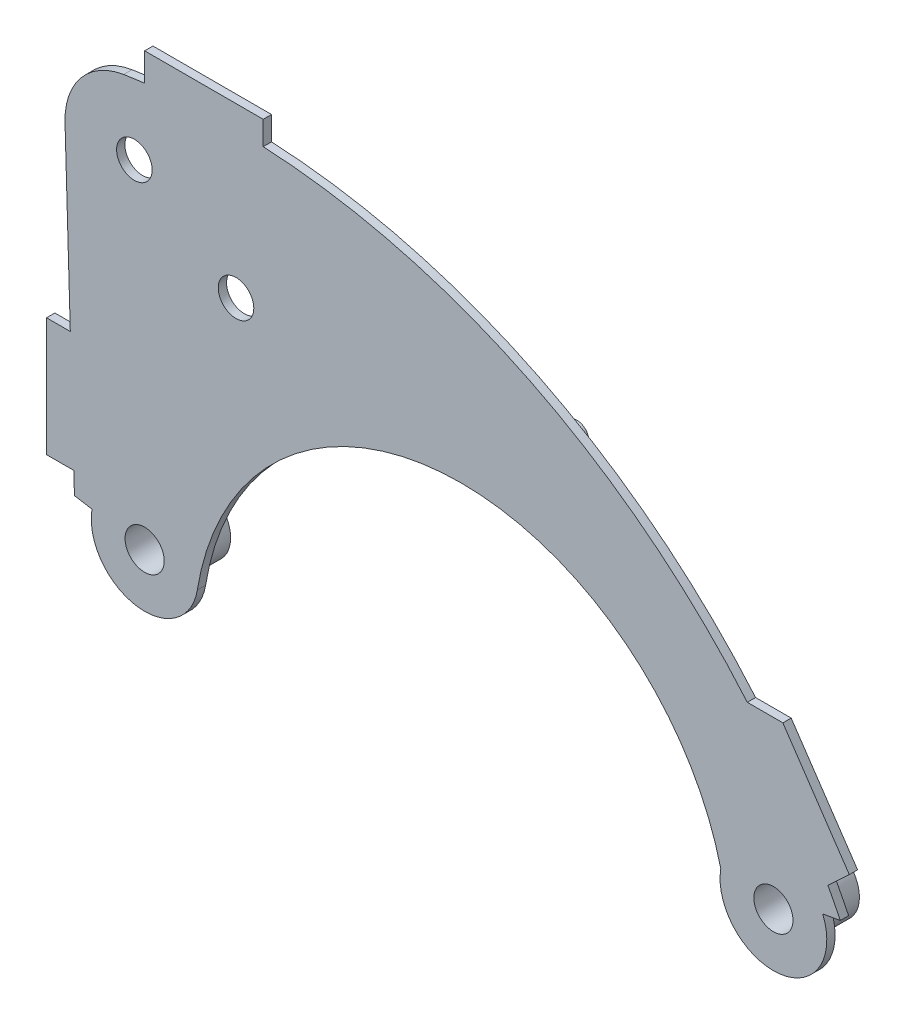
SolidWorks part; units mm, degrees
ref_plane "Front Plane" through (0, 0, 0) normal (0, 0, 1) x (1, 0, 0)
ref_plane "Top Plane" through (0, 0, 0) normal (0, 1, 0) x (1, 0, 0)
ref_plane "Right Plane" through (0, 0, 0) normal (1, 0, 0) x (0, 0, -1)
sketch "Sketch1" plane through (0, 0, 0) normal (0, 0, 1) x (1, 0, 0)
  line L0 (3.5714, 20.1522) -> (3.5714, -246.7943) construction
  line L1 (-308.017, 51.5444) -> (-322.8113, 54.0201)
  line L2 (3.2114, 1.0414) -> (684.3791, 1.0414) construction
  line L3 (3.2114, 1.0414) -> (-642.1053, 1.0414) construction
  line L4 (3.2114, 1.0414) -> (3.2114, 295.5408) construction
  line L5 (266.5683, 46.7848) -> (266.5683, 1.7848) construction
  line L6 (3.2114, 1.0414) -> (3.5714, 1.1081) construction
  line L7 (-263.6341, 44.1172) -> (-263.6341, -0.8828) construction
  line L8 (308.1159, 64.0706) -> (322.9429, 66.6583)
  line L9 (-263.6341, -0.8828) -> (3.2114, 1.0414)
  line L10 (-322.8113, 54.0201) -> (-330.7613, 322.7691)
  line L11 (3.2114, 1.0414) -> (3.5714, 1.1081)
  arc A0 (222.17, 54.1191) -> (-219.2092, 36.9459) centre (3.2114, 1.0414) ccw
  arc A1 (-308.017, 51.5444) -> (-219.2092, 36.9459) centre (-263.6341, 44.1172) ccw
  arc A4 (222.17, 54.1191) -> (308.1159, 64.0706) centre (266.5683, 46.7848) ccw
  circle A5 centre (-263.6341, 44.1172) radius 16.5
  circle A6 centre (266.5683, 46.7848) radius 16.5
  circle A9 centre (3.2114, 1.0414) radius 217.3
  arc A11 (-281.3271, 382.2962) -> (-330.7613, 322.7691) centre (-272.2869, 324.4989) ccw
  circle A12 centre (-272.2869, 324.4989) radius 15
  arc A14 (322.9429, 66.6583) -> (-281.3271, 382.2962) centre (-192.7071, -184.2846) ccw
  circle A15 centre (-186.5844, 266.4702) radius 15
  dimension "D1" = 90
  dimension "D2" = 0.413
  dimension "D5" = 10.5
  dimension "D6" = 267.3
extrude "Boss-Extrude3" add sketch "Sketch1" along normal blind 7 contours L8 A14 A11 A15 L10 L1 A1 A0 A4 A5 A6 | A11 A12
sketch "Sketch2" plane through (0, 0, 7) normal (0, 0, 1) x (1, 0, 0)
  circle A0 centre (-263.6341, 44.1172) radius 27.5
  circle A2 centre (-263.6341, 44.1172) radius 16.5
  circle A3 centre (266.5683, 46.7848) radius 16.5
  circle A4 centre (266.5683, 46.7848) radius 27.5
extrude "Boss-Extrude4" add sketch "Sketch2" against normal blind 45
sketch "Sketch3" plane through (0, 0, 0) normal (0, 0, -1) x (-1, 0, 0)
  line L0 (-198.3557, 159.2041) -> (-104.6899, 234.2155)
  arc A0 (-198.3557, 159.2041) -> (-104.6899, 234.2155) centre (-151.5228, 196.7098) cw
  arc A1 (281.3271, 382.2962) -> (-322.9429, 66.6583) centre (192.7071, -184.2846) ccw construction
sketch "Sketch4" plane through (0, 0, 0) normal (0, 0, -1) x (-1, 0, 0)
  line L0 (0, 0) -> (-425.4069, 0) construction
  circle A5 centre (-73.9774, 283.9594) radius 10
  circle A6 centre (77.0706, 306.7937) radius 10
  circle A7 centre (0, 304.7312) radius 13
  point P11 (0, 304.7312)
  point P13 (-73.9774, 283.9594)
  point P14 (77.0706, 306.7937)
extrude "Boss-Extrude10" add sketch "Sketch4" along normal blind 20
sketch "Sketch5" plane through (0, 0, 0) normal (0, 0, -1) x (-1, 0, 0)
  line L0 (-335.894, 46.7848) -> (-266.5683, 46.7848) construction
  line L1 (-266.5683, 46.7848) -> (-266.5683, 327.4295) construction
  line L2 (-266.5683, 86.7848) -> (-312.1324, 86.7848) construction
  line L3 (-312.1324, 86.7848) -> (-311.3643, 88.2148)
  dimension "D1" = 40
sketch "Sketch6" plane through (0, 0, 0) normal (0, 0, -1) x (-1, 0, 0)
  line L2 (-244.5283, 186.7848) -> (-312.1324, 86.7848)
  line L3 (-274.5283, 186.7848) -> (-244.5283, 186.7848)
  line L4 (-274.5283, 186.7848) -> (-330.5348, 103.9399)
  line L5 (-330.5348, 103.9399) -> (-312.1324, 86.7848)
  arc A0 (281.3271, 382.2962) -> (-322.9429, 66.6583) centre (192.7071, -184.2846) ccw construction
extrude "Boss-Extrude11" add sketch "Sketch6" against normal up to surface (7 mm away) contours L3 L2 L5 L4 up to face at (-171.5844, 266.4702, 7)
sketch "Sketch7" plane through (0, 0, -38) normal (0, 0, -1) x (-1, 0, 0)
  line L0 (263.6341, 44.1172) -> (263.6341, 172.1603) construction
  line L1 (263.6341, 172.1603) -> (263.6341, 44.1172) construction
  line L2 (263.6341, 44.1172) -> (392.9662, 44.1172) construction
sketch "Sketch9" plane through (0, 0, 0) normal (0, 0, -1) x (-1, 0, 0)
  line L0 (326.3061, 172.1603) -> (346.3061, 172.1603)
  line L1 (322.8113, 54.0201) -> (330.7613, 322.7691) construction
  line L2 (346.3061, 172.1603) -> (346.3061, 72.1603)
  line L3 (346.3061, 72.1603) -> (323.3479, 72.1603)
  line L4 (326.3061, 172.1603) -> (323.3479, 72.1603)
extrude "Boss-Extrude12" add sketch "Sketch9" against normal up to surface (7 mm away) up to face at (2.518, 127.0528, 7)
sketch "Sketch10" plane through (0, 0, 0) normal (0, 0, -1) x (-1, 0, 0)
  line L0 (163.6341, 388.4475) -> (163.6341, 408.4475)
  line L1 (163.6341, 408.4475) -> (263.6341, 408.4475)
  line L3 (263.6341, 384.1731) -> (163.6341, 388.4475)
  line L5 (263.6341, 384.1731) -> (263.6341, 408.4475)
  line L6 (263.6341, 44.1172) -> (263.6341, 172.1603) construction
  arc A1 (281.3271, 382.2962) -> (-244.5283, 186.7848) centre (192.7071, -184.2846) ccw construction
extrude "Boss-Extrude13" add sketch "Sketch10" against normal up to surface (7 mm away) up to face at (-72.6119, 125.9656, 7)
